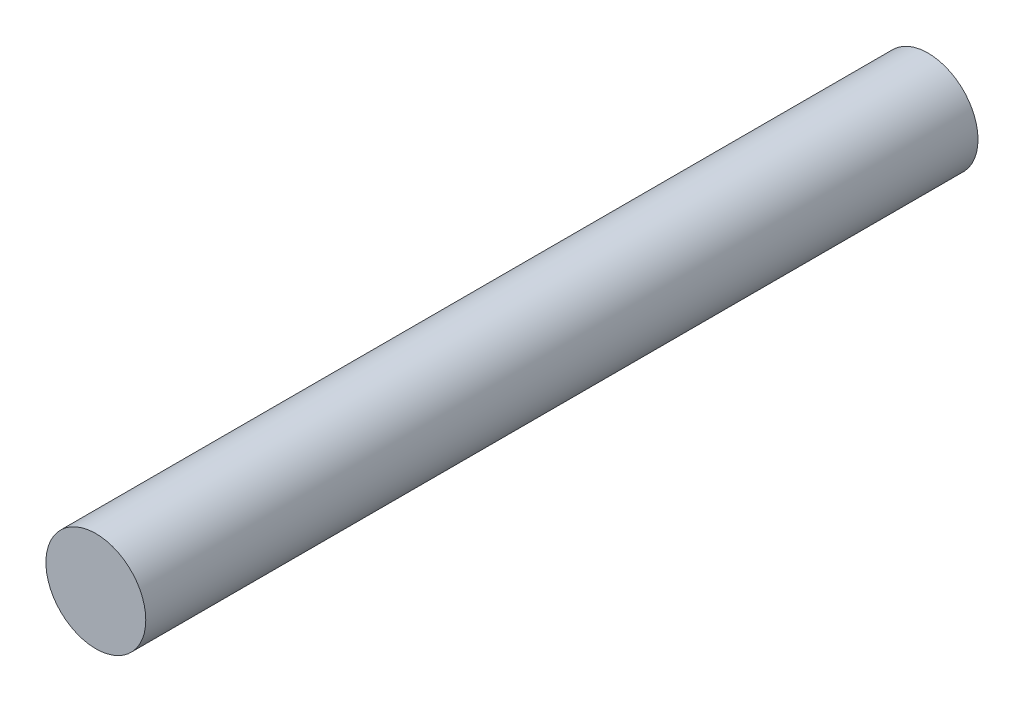
SolidWorks part; units mm, degrees
ref_plane "Alzado" through (0, 0, 0) normal (0, 0, 1) x (1, 0, 0)
ref_plane "Planta" through (0, 0, 0) normal (0, 1, 0) x (1, 0, 0)
ref_plane "Vista lateral" through (0, 0, 0) normal (1, 0, 0) x (0, 0, -1)
sketch "Croquis1" plane through (0, 0, 0) normal (0, 0, 1) x (1, 0, 0)
  circle A0 centre (0, 0) radius 3
  dimension "D1" = 6
extrude "Saliente-Extruir1" add sketch "Croquis1" along normal blind 50
